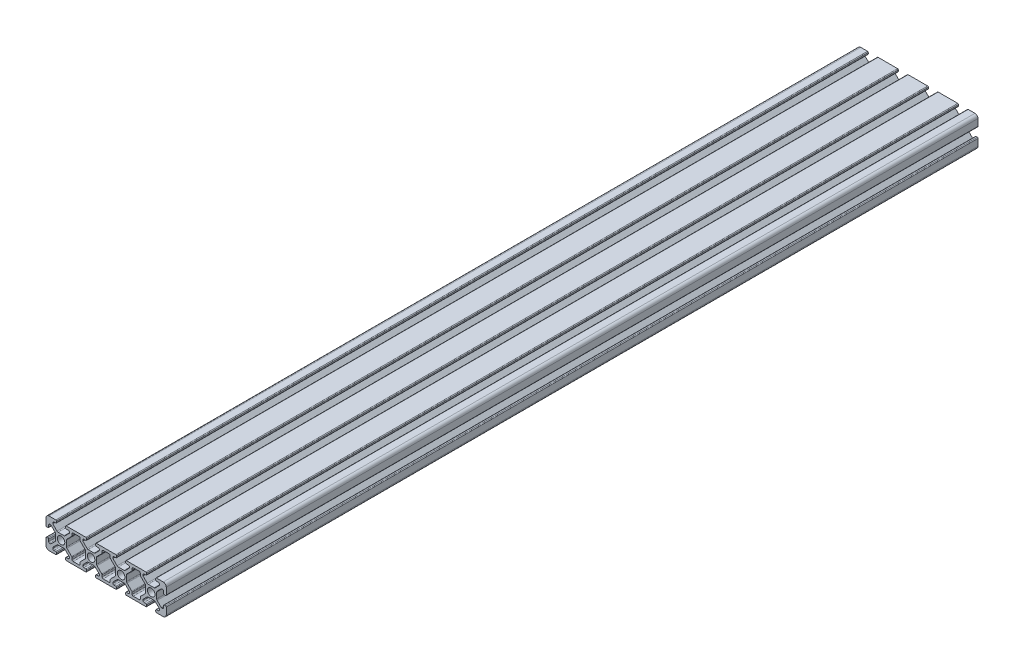
SolidWorks part; units mm, degrees
material "6063-T5"
ref_plane "Front Plane" through (0, 0, 0) normal (0, 0, 1) x (1, 0, 0)
ref_plane "Top Plane" through (0, 0, 0) normal (0, 1, 0) x (1, 0, 0)
ref_plane "Right Plane" through (0, 0, 0) normal (1, 0, 0) x (0, 0, -1)
sketch "Sketch1" plane through (0, 0, 0) normal (0, 0, 1) x (1, 0, 0)
  line L0 (2, 0) -> (6.5, 0)
  line L1 (80, 2) -> (80, 6.5)
  line L2 (78, 20) -> (73.5, 20)
  line L3 (0, 18) -> (0, 13.5)
  line L4 (33, 19.5) -> (33, 18.7)
  line L5 (27, 19.5) -> (27, 18.7)
  line L6 (7, 19.5) -> (7, 18.7)
  line L7 (13, 19.5) -> (13, 18.7)
  line L8 (6.5, 20) -> (2, 20)
  line L9 (53, 19.5) -> (53, 18.7)
  line L10 (47, 19.5) -> (47, 18.7)
  line L11 (73, 19.5) -> (73, 18.7)
  line L12 (67, 19.5) -> (67, 18.7)
  line L13 (33, 1.3) -> (33, 0.5)
  line L14 (27, 1.3) -> (27, 0.5)
  line L15 (53, 1.3) -> (53, 0.5)
  line L16 (47, 1.3) -> (47, 0.5)
  line L17 (73, 1.3) -> (73, 0.5)
  line L18 (67, 1.3) -> (67, 0.5)
  line L19 (13, 1.3) -> (13, 0.5)
  line L20 (7, 1.3) -> (7, 0.5)
  line L21 (13.5, 20) -> (26.5, 20) construction
  line L22 (26.5, 20) -> (13.5, 20)
  line L23 (46.5, 20) -> (33.5, 20)
  line L24 (66.5, 20) -> (53.5, 20)
  line L25 (73.5, 0) -> (78, 0)
  line L26 (53.5, 0) -> (66.5, 0)
  line L27 (33.5, 0) -> (46.5, 0)
  line L28 (13.5, 0) -> (26.5, 0)
  line L29 (79.5, 13) -> (78.7, 13)
  line L30 (79.5, 7) -> (78.7, 7)
  line L31 (0.5, 13) -> (1.3, 13)
  line L32 (0.5, 7) -> (1.3, 7)
  line L33 (0, 6.5) -> (0, 2)
  line L34 (80, 13.5) -> (80, 18)
  line L35 (1.8, 13.5) -> (1.8, 14.75)
  line L36 (5.25, 18.2) -> (6.5, 18.2)
  line L37 (78.2, 14.75) -> (78.2, 13.5)
  line L38 (74.75, 1.8) -> (73.5, 1.8)
  line L39 (1.8, 5.25) -> (1.8, 6.5)
  line L40 (13.5, 18.2) -> (14.75, 18.2)
  line L41 (6.5, 1.8) -> (5.25, 1.8)
  line L42 (33.5, 18.2) -> (34.75, 18.2)
  line L43 (26.5, 1.8) -> (25.25, 1.8)
  line L44 (53.5, 18.2) -> (54.75, 18.2)
  line L45 (46.5, 1.8) -> (45.25, 1.8)
  line L46 (73.5, 18.2) -> (74.75, 18.2)
  line L47 (66.5, 1.8) -> (65.25, 1.8)
  line L48 (78.2, 6.5) -> (78.2, 5.25)
  line L49 (12.6701, 13.9429) -> (15.5, 16.7728)
  line L50 (12.6701, 6.0571) -> (15.5, 3.2272)
  line L51 (32.6701, 13.9429) -> (35.5, 16.7728)
  line L52 (33.9429, 12.6701) -> (37.0803, 15.8075)
  line L53 (27.3299, 13.9429) -> (24.5, 16.7728)
  line L54 (22.9197, 15.8075) -> (26.0571, 12.6701)
  line L55 (27.3299, 6.0571) -> (24.5, 3.2272)
  line L56 (22.9197, 4.1925) -> (26.0571, 7.3299)
  line L57 (47.3299, 13.9429) -> (44.5, 16.7728)
  line L58 (42.9197, 15.8075) -> (46.0571, 12.6701)
  line L59 (47.3299, 6.0571) -> (44.5, 3.2272)
  line L60 (42.9197, 4.1925) -> (46.0571, 7.3299)
  line L61 (67.3299, 13.9429) -> (64.5, 16.7728)
  line L62 (62.9197, 15.8075) -> (66.0571, 12.6701)
  line L63 (67.3299, 6.0571) -> (64.5, 3.2272)
  line L64 (62.9197, 4.1925) -> (66.0571, 7.3299)
  line L65 (33.9429, 7.3299) -> (37.0803, 4.1925)
  line L66 (13.9429, 12.6701) -> (17.0803, 15.8075)
  line L67 (6.0571, 7.3299) -> (3.2272, 4.5)
  line L68 (7.3299, 6.0571) -> (4.5, 3.2272)
  line L69 (7.3299, 13.9429) -> (4.5, 16.7728)
  line L70 (32.6701, 6.0571) -> (35.5, 3.2272)
  line L71 (13.9429, 7.3299) -> (17.0803, 4.1925)
  line L72 (52.6701, 13.9429) -> (55.5, 16.7728)
  line L73 (6.0571, 12.6701) -> (3.2272, 15.5)
  line L74 (53.9429, 12.6701) -> (57.0803, 15.8075)
  line L75 (53.9429, 7.3299) -> (57.0803, 4.1925)
  line L76 (52.6701, 6.0571) -> (55.5, 3.2272)
  line L77 (72.6701, 13.9429) -> (75.5, 16.7728)
  line L78 (73.9429, 12.6701) -> (76.7728, 15.5)
  line L79 (73.9429, 7.3299) -> (76.7728, 4.5)
  line L80 (72.6701, 6.0571) -> (75.5, 3.2272)
  line L81 (28.037, 13.65) -> (31.963, 13.65)
  line L82 (18.05, 18.2) -> (21.95, 18.2)
  line L83 (14.75, 1.8) -> (13.5, 1.8)
  line L84 (15.5, 17.45) -> (15.5, 16.7728)
  line L85 (34.75, 1.8) -> (33.5, 1.8)
  line L86 (4.5, 17.45) -> (4.5, 16.7728)
  line L87 (54.75, 1.8) -> (53.5, 1.8)
  line L88 (24.5, 17.45) -> (24.5, 16.7728)
  line L89 (27.7144, 8.9872) -> (21.8, 3.0728) [skipped]
  line L90 (25.25, 18.2) -> (26.5, 18.2)
  line L91 (27.7144, 11.0128) -> (21.8, 16.9272) [skipped]
  line L92 (45.25, 18.2) -> (46.5, 18.2)
  line L93 (33.65, 11.963) -> (33.65, 8.037)
  line L94 (31.963, 6.35) -> (28.037, 6.35)
  line L95 (26.35, 8.037) -> (26.35, 11.963)
  line L96 (65.25, 18.2) -> (66.5, 18.2)
  line L97 (44.5, 17.45) -> (44.5, 16.7728)
  line L98 (35.5, 17.45) -> (35.5, 16.7728)
  line L99 (47.7144, 8.9872) -> (41.8, 3.0728) [skipped]
  line L100 (47.7144, 11.0128) -> (41.8, 16.9272) [skipped]
  line L101 (67.7144, 11.0128) -> (61.8, 16.9272) [skipped]
  line L102 (67.7144, 8.9872) -> (61.8, 3.0728) [skipped]
  line L103 (13.65, 11.963) -> (13.65, 8.037)
  line L104 (11.963, 6.35) -> (8.037, 6.35)
  line L105 (6.35, 8.037) -> (6.35, 11.963)
  line L106 (8.037, 13.65) -> (11.963, 13.65)
  line L107 (48.037, 13.65) -> (51.963, 13.65)
  line L108 (53.65, 11.963) -> (53.65, 8.037)
  line L109 (51.963, 6.35) -> (48.037, 6.35)
  line L110 (46.35, 8.037) -> (46.35, 11.963)
  line L111 (68.037, 13.65) -> (71.963, 13.65)
  line L112 (73.65, 11.963) -> (73.65, 8.037)
  line L113 (71.963, 6.35) -> (68.037, 6.35)
  line L114 (66.35, 8.037) -> (66.35, 11.963)
  line L115 (64.5, 17.45) -> (64.5, 16.7728)
  line L116 (55.5, 17.45) -> (55.5, 16.7728)
  line L117 (4.5, 2.55) -> (4.5, 3.2272)
  line L118 (75.5, 17.45) -> (75.5, 16.7728)
  line L119 (24.5, 2.55) -> (24.5, 3.2272)
  line L120 (15.5, 2.55) -> (15.5, 3.2272)
  line L121 (44.5, 2.55) -> (44.5, 3.2272)
  line L122 (35.5, 2.55) -> (35.5, 3.2272)
  line L123 (64.5, 2.55) -> (64.5, 3.2272)
  line L124 (55.5, 2.55) -> (55.5, 3.2272)
  line L125 (2.55, 15.5) -> (3.2272, 15.5)
  line L126 (75.5, 2.55) -> (75.5, 3.2272)
  line L127 (2.55, 4.5) -> (3.2272, 4.5)
  line L128 (77.45, 15.5) -> (76.7728, 15.5)
  line L129 (17.3, 17.45) -> (17.3, 16.3379)
  line L130 (77.45, 4.5) -> (76.7728, 4.5)
  line L131 (22.7, 17.45) -> (22.7, 16.3379)
  line L132 (38.05, 18.2) -> (41.95, 18.2)
  line L133 (37.3, 17.45) -> (37.3, 16.3379)
  line L134 (42.7, 17.45) -> (42.7, 16.3379)
  line L135 (58.05, 18.2) -> (61.95, 18.2)
  line L136 (57.3, 17.45) -> (57.3, 16.3379)
  line L137 (62.7, 17.45) -> (62.7, 16.3379)
  line L138 (17.3, 3.6621) -> (17.3, 2.55)
  line L139 (18.05, 1.8) -> (21.95, 1.8)
  line L140 (22.7, 2.55) -> (22.7, 3.6621)
  line L141 (37.3, 3.6621) -> (37.3, 2.55)
  line L142 (38.05, 1.8) -> (41.95, 1.8)
  line L143 (42.7, 2.55) -> (42.7, 3.6621)
  line L144 (57.3, 3.6621) -> (57.3, 2.55)
  line L145 (58.05, 1.8) -> (61.95, 1.8)
  line L146 (62.7, 2.55) -> (62.7, 3.6621)
  circle A0 centre (10, 10) radius 2.5
  circle A1 centre (30, 10) radius 2.5
  circle A2 centre (50, 10) radius 2.5
  circle A3 centre (70, 10) radius 2.5
  arc A4 (78, 0) -> (80, 2) centre (78, 2) ccw
  arc A5 (80, 18) -> (78, 20) centre (78, 18) ccw
  arc A6 (2, 0) -> (0, 2) centre (2, 2) cw
  arc A7 (2, 20) -> (0, 18) centre (2, 18) ccw
  arc A8 (12.6701, 13.9429) -> (11.963, 13.65) centre (11.963, 14.65) cw
  arc A9 (7.3299, 13.9429) -> (8.037, 13.65) centre (8.037, 14.65) ccw
  arc A10 (6.0571, 12.6701) -> (6.35, 11.963) centre (5.35, 11.963) cw
  arc A11 (6.0571, 7.3299) -> (6.35, 8.037) centre (5.35, 8.037) ccw
  arc A12 (7.3299, 6.0571) -> (8.037, 6.35) centre (8.037, 5.35) cw
  arc A13 (12.6701, 6.0571) -> (11.963, 6.35) centre (11.963, 5.35) ccw
  arc A14 (32.6701, 6.0571) -> (31.963, 6.35) centre (31.963, 5.35) ccw
  arc A15 (27.3299, 6.0571) -> (28.037, 6.35) centre (28.037, 5.35) cw
  arc A16 (27.3299, 13.9429) -> (28.037, 13.65) centre (28.037, 14.65) ccw
  arc A17 (32.6701, 13.9429) -> (31.963, 13.65) centre (31.963, 14.65) cw
  arc A18 (47.3299, 6.0571) -> (48.037, 6.35) centre (48.037, 5.35) cw
  arc A19 (52.6701, 6.0571) -> (51.963, 6.35) centre (51.963, 5.35) ccw
  arc A20 (52.6701, 13.9429) -> (51.963, 13.65) centre (51.963, 14.65) cw
  arc A21 (47.3299, 13.9429) -> (48.037, 13.65) centre (48.037, 14.65) ccw
  arc A22 (72.6701, 13.9429) -> (71.963, 13.65) centre (71.963, 14.65) cw
  arc A23 (67.3299, 13.9429) -> (68.037, 13.65) centre (68.037, 14.65) ccw
  arc A24 (67.3299, 6.0571) -> (68.037, 6.35) centre (68.037, 5.35) cw
  arc A25 (72.6701, 6.0571) -> (71.963, 6.35) centre (71.963, 5.35) ccw
  arc A26 (73.9429, 7.3299) -> (73.65, 8.037) centre (74.65, 8.037) cw
  arc A27 (73.9429, 12.6701) -> (73.65, 11.963) centre (74.65, 11.963) ccw
  arc A28 (66.0571, 7.3299) -> (66.35, 8.037) centre (65.35, 8.037) ccw
  arc A29 (66.0571, 12.6701) -> (66.35, 11.963) centre (65.35, 11.963) cw
  arc A30 (53.9429, 7.3299) -> (53.65, 8.037) centre (54.65, 8.037) cw
  arc A31 (53.9429, 12.6701) -> (53.65, 11.963) centre (54.65, 11.963) ccw
  arc A32 (78.2, 14.75) -> (77.45, 15.5) centre (77.45, 14.75) ccw
  arc A33 (75.5, 17.45) -> (74.75, 18.2) centre (74.75, 17.45) ccw
  arc A34 (78.2, 5.25) -> (77.45, 4.5) centre (77.45, 5.25) cw
  arc A35 (75.5, 2.55) -> (74.75, 1.8) centre (74.75, 2.55) cw
  arc A36 (46.0571, 7.3299) -> (46.35, 8.037) centre (45.35, 8.037) ccw
  arc A37 (46.0571, 12.6701) -> (46.35, 11.963) centre (45.35, 11.963) cw
  arc A38 (33.9429, 7.3299) -> (33.65, 8.037) centre (34.65, 8.037) cw
  arc A39 (33.9429, 12.6701) -> (33.65, 11.963) centre (34.65, 11.963) ccw
  arc A40 (13.9429, 12.6701) -> (13.65, 11.963) centre (14.65, 11.963) ccw
  arc A41 (13.9429, 7.3299) -> (13.65, 8.037) centre (14.65, 8.037) cw
  arc A42 (26.0571, 7.3299) -> (26.35, 8.037) centre (25.35, 8.037) ccw
  arc A43 (26.0571, 12.6701) -> (26.35, 11.963) centre (25.35, 11.963) cw
  arc A44 (65.25, 1.8) -> (64.5, 2.55) centre (65.25, 2.55) cw
  arc A45 (61.95, 1.8) -> (62.7, 2.55) centre (61.95, 2.55) ccw
  arc A46 (57.3, 2.55) -> (58.05, 1.8) centre (58.05, 2.55) ccw
  arc A47 (54.75, 1.8) -> (55.5, 2.55) centre (54.75, 2.55) ccw
  arc A48 (45.25, 1.8) -> (44.5, 2.55) centre (45.25, 2.55) cw
  arc A49 (64.5, 17.45) -> (65.25, 18.2) centre (65.25, 17.45) cw
  arc A50 (61.95, 18.2) -> (62.7, 17.45) centre (61.95, 17.45) cw
  arc A51 (58.05, 18.2) -> (57.3, 17.45) centre (58.05, 17.45) ccw
  arc A52 (53, 18.7) -> (53.5, 18.2) centre (53.5, 18.7) ccw
  arc A53 (53, 19.5) -> (53.5, 20) centre (53.5, 19.5) cw
  arc A54 (67, 18.7) -> (66.5, 18.2) centre (66.5, 18.7) cw
  arc A55 (67, 19.5) -> (66.5, 20) centre (66.5, 19.5) ccw
  arc A56 (73, 18.7) -> (73.5, 18.2) centre (73.5, 18.7) ccw
  arc A57 (73, 19.5) -> (73.5, 20) centre (73.5, 19.5) cw
  arc A58 (78.7, 13) -> (78.2, 13.5) centre (78.7, 13.5) cw
  arc A59 (79.5, 13) -> (80, 13.5) centre (79.5, 13.5) ccw
  arc A60 (78.7, 7) -> (78.2, 6.5) centre (78.7, 6.5) ccw
  arc A61 (79.5, 7) -> (80, 6.5) centre (79.5, 6.5) cw
  arc A62 (73, 0.5) -> (73.5, 0) centre (73.5, 0.5) ccw
  arc A63 (73, 1.3) -> (73.5, 1.8) centre (73.5, 1.3) cw
  arc A64 (67, 0.5) -> (66.5, 0) centre (66.5, 0.5) cw
  arc A65 (67, 1.3) -> (66.5, 1.8) centre (66.5, 1.3) ccw
  arc A66 (53, 0.5) -> (53.5, 0) centre (53.5, 0.5) ccw
  arc A67 (53, 1.3) -> (53.5, 1.8) centre (53.5, 1.3) cw
  arc A68 (47, 0.5) -> (46.5, 0) centre (46.5, 0.5) cw
  arc A69 (47, 1.3) -> (46.5, 1.8) centre (46.5, 1.3) ccw
  arc A70 (33, 0.5) -> (33.5, 0) centre (33.5, 0.5) ccw
  arc A71 (33, 1.3) -> (33.5, 1.8) centre (33.5, 1.3) cw
  arc A72 (27, 0.5) -> (26.5, 0) centre (26.5, 0.5) cw
  arc A73 (27, 1.3) -> (26.5, 1.8) centre (26.5, 1.3) ccw
  arc A74 (47, 18.7) -> (46.5, 18.2) centre (46.5, 18.7) cw
  arc A75 (47, 19.5) -> (46.5, 20) centre (46.5, 19.5) ccw
  arc A76 (33, 18.7) -> (33.5, 18.2) centre (33.5, 18.7) ccw
  arc A77 (33, 19.5) -> (33.5, 20) centre (33.5, 19.5) cw
  arc A78 (27, 18.7) -> (26.5, 18.2) centre (26.5, 18.7) cw
  arc A79 (27, 19.5) -> (26.5, 20) centre (26.5, 19.5) ccw
  arc A80 (13, 18.7) -> (13.5, 18.2) centre (13.5, 18.7) ccw
  arc A81 (13.5, 20) -> (13, 19.5) centre (13.5, 19.5) ccw
  arc A82 (13, 0.5) -> (13.5, 0) centre (13.5, 0.5) ccw
  arc A83 (13, 1.3) -> (13.5, 1.8) centre (13.5, 1.3) cw
  arc A84 (7, 0.5) -> (6.5, 0) centre (6.5, 0.5) cw
  arc A85 (7, 1.3) -> (6.5, 1.8) centre (6.5, 1.3) ccw
  arc A86 (0, 6.5) -> (0.5, 7) centre (0.5, 6.5) cw
  arc A87 (1.3, 7) -> (1.8, 6.5) centre (1.3, 6.5) cw
  arc A88 (0, 13.5) -> (0.5, 13) centre (0.5, 13.5) ccw
  arc A89 (1.3, 13) -> (1.8, 13.5) centre (1.3, 13.5) ccw
  arc A90 (6.5, 20) -> (7, 19.5) centre (6.5, 19.5) cw
  arc A91 (7, 18.7) -> (6.5, 18.2) centre (6.5, 18.7) cw
  arc A92 (55.5, 17.45) -> (54.75, 18.2) centre (54.75, 17.45) ccw
  arc A93 (44.5, 17.45) -> (45.25, 18.2) centre (45.25, 17.45) cw
  arc A94 (37.3, 2.55) -> (38.05, 1.8) centre (38.05, 2.55) ccw
  arc A95 (38.05, 18.2) -> (37.3, 17.45) centre (38.05, 17.45) ccw
  arc A96 (41.95, 18.2) -> (42.7, 17.45) centre (41.95, 17.45) cw
  arc A97 (41.95, 1.8) -> (42.7, 2.55) centre (41.95, 2.55) ccw
  arc A98 (34.75, 1.8) -> (35.5, 2.55) centre (34.75, 2.55) ccw
  arc A99 (25.25, 1.8) -> (24.5, 2.55) centre (25.25, 2.55) cw
  arc A100 (14.75, 1.8) -> (15.5, 2.55) centre (14.75, 2.55) ccw
  arc A101 (5.25, 1.8) -> (4.5, 2.55) centre (5.25, 2.55) cw
  arc A102 (2.55, 4.5) -> (1.8, 5.25) centre (2.55, 5.25) cw
  arc A103 (1.8, 14.75) -> (2.55, 15.5) centre (2.55, 14.75) cw
  arc A104 (24.5, 17.45) -> (25.25, 18.2) centre (25.25, 17.45) cw
  arc A105 (34.75, 18.2) -> (35.5, 17.45) centre (34.75, 17.45) cw
  arc A106 (21.95, 18.2) -> (22.7, 17.45) centre (21.95, 17.45) cw
  arc A107 (18.05, 18.2) -> (17.3, 17.45) centre (18.05, 17.45) ccw
  arc A108 (15.5, 17.45) -> (14.75, 18.2) centre (14.75, 17.45) ccw
  arc A109 (5.25, 18.2) -> (4.5, 17.45) centre (5.25, 17.45) ccw
  arc A110 (62.7, 3.6621) -> (62.9197, 4.1925) centre (63.45, 3.6621) cw
  arc A111 (57.3, 3.6621) -> (57.0803, 4.1925) centre (56.55, 3.6621) ccw
  arc A112 (62.7, 16.3379) -> (62.9197, 15.8075) centre (63.45, 16.3379) ccw
  arc A113 (57.3, 16.3379) -> (57.0803, 15.8075) centre (56.55, 16.3379) cw
  arc A114 (42.7, 3.6621) -> (42.9197, 4.1925) centre (43.45, 3.6621) cw
  arc A115 (37.3, 3.6621) -> (37.0803, 4.1925) centre (36.55, 3.6621) ccw
  arc A116 (42.7, 16.3379) -> (42.9197, 15.8075) centre (43.45, 16.3379) ccw
  arc A117 (37.3, 16.3379) -> (37.0803, 15.8075) centre (36.55, 16.3379) cw
  arc A118 (22.7, 16.3379) -> (22.9197, 15.8075) centre (23.45, 16.3379) ccw
  arc A119 (17.3, 16.3379) -> (17.0803, 15.8075) centre (16.55, 16.3379) cw
  arc A120 (17.3, 3.6621) -> (17.0803, 4.1925) centre (16.55, 3.6621) ccw
  arc A121 (22.7, 3.6621) -> (22.9197, 4.1925) centre (23.45, 3.6621) cw
  arc A122 (21.95, 1.8) -> (22.7, 2.55) centre (21.95, 2.55) ccw
  arc A123 (17.3, 2.55) -> (18.05, 1.8) centre (18.05, 2.55) ccw
  point P124 (0, 0)
  point P394 (17.3, 16.0272)
  dimension "D1" = 4
  dimension "D3" = 4
  dimension "D2" = 2
  dimension "D4" = 3
extrude "Boss-Extrude1" add sketch "Sketch1" along normal mid plane 540
